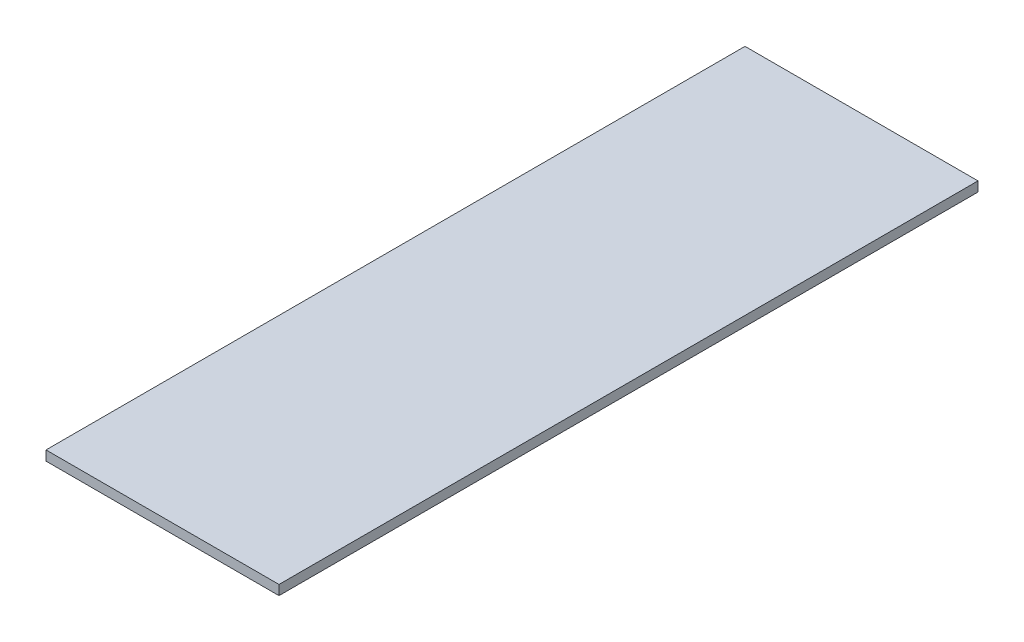
SolidWorks part; units mm, degrees
material "Oak"
ref_plane "Front Plane" through (0, 0, 0) normal (0, 0, 1) x (1, 0, 0)
ref_plane "Top Plane" through (0, 0, 0) normal (0, 1, 0) x (1, 0, 0)
ref_plane "Right Plane" through (0, 0, 0) normal (1, 0, 0) x (0, 0, -1)
sketch "Sketch1" plane through (0, 0, 0) normal (0, 1, 0) x (1, 0, 0)
  line L1 (-152.4, -457.2) -> (152.4, -457.2)
  line L2 (-152.4, -457.2) -> (-152.4, 457.2)
  line L3 (-152.4, 457.2) -> (152.4, 457.2)
  line L4 (152.4, -457.2) -> (152.4, 457.2)
  line L5 (-152.4, -457.2) -> (152.4, 457.2) construction
  line L6 (-152.4, 457.2) -> (152.4, -457.2) construction
  point P0 (0, 0)
  dimension "D1" = 304.8
  dimension "D2" = 914.4
extrude "Boss-Extrude1" add sketch "Sketch1" along normal mid plane 12.7
